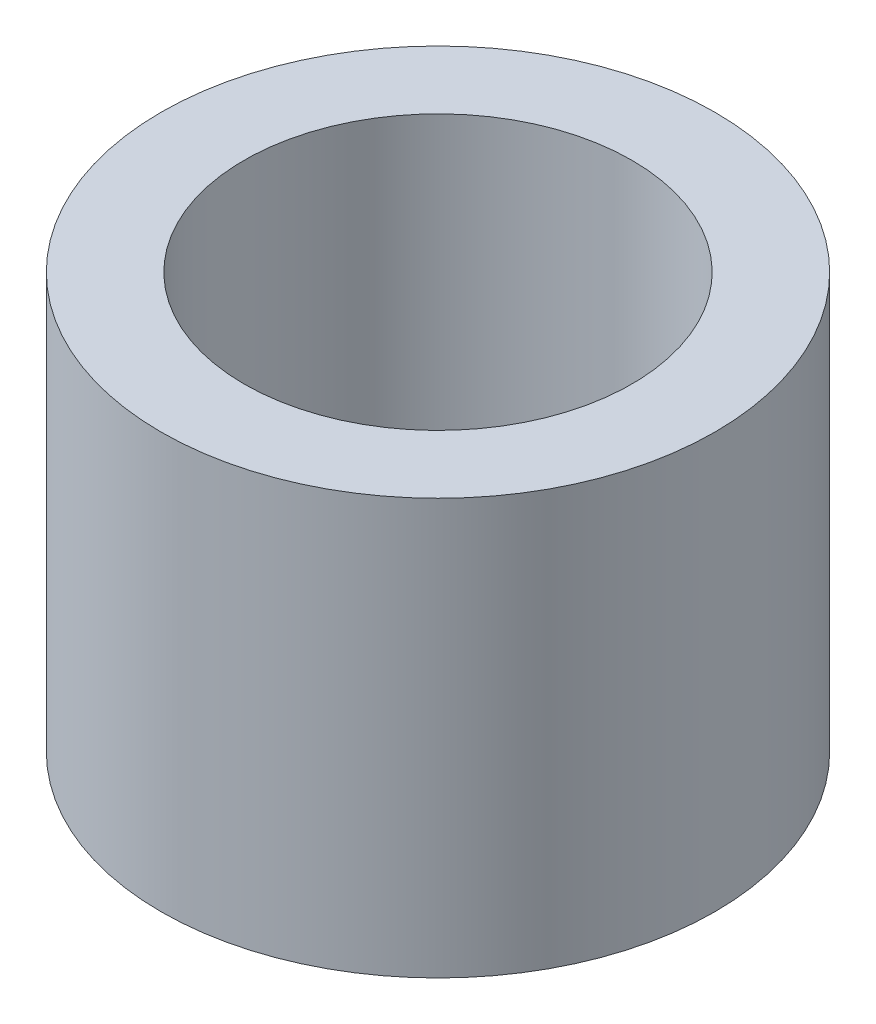
SolidWorks part; units mm, degrees
ref_plane "Front Plane" through (0, 0, 0) normal (0, 0, 1) x (1, 0, 0)
ref_plane "Top Plane" through (0, 0, 0) normal (0, 1, 0) x (1, 0, 0)
ref_plane "Right Plane" through (0, 0, 0) normal (1, 0, 0) x (0, 0, -1)
sketch "Sketch1" plane through (0, 0, 0) normal (0, 1, 0) x (1, 0, 0)
  circle A0 centre (0, 0) radius 3.5
  circle A1 centre (0, 0) radius 5
extrude "Boss-Extrude1" add sketch "Sketch1" along normal blind 7.5
